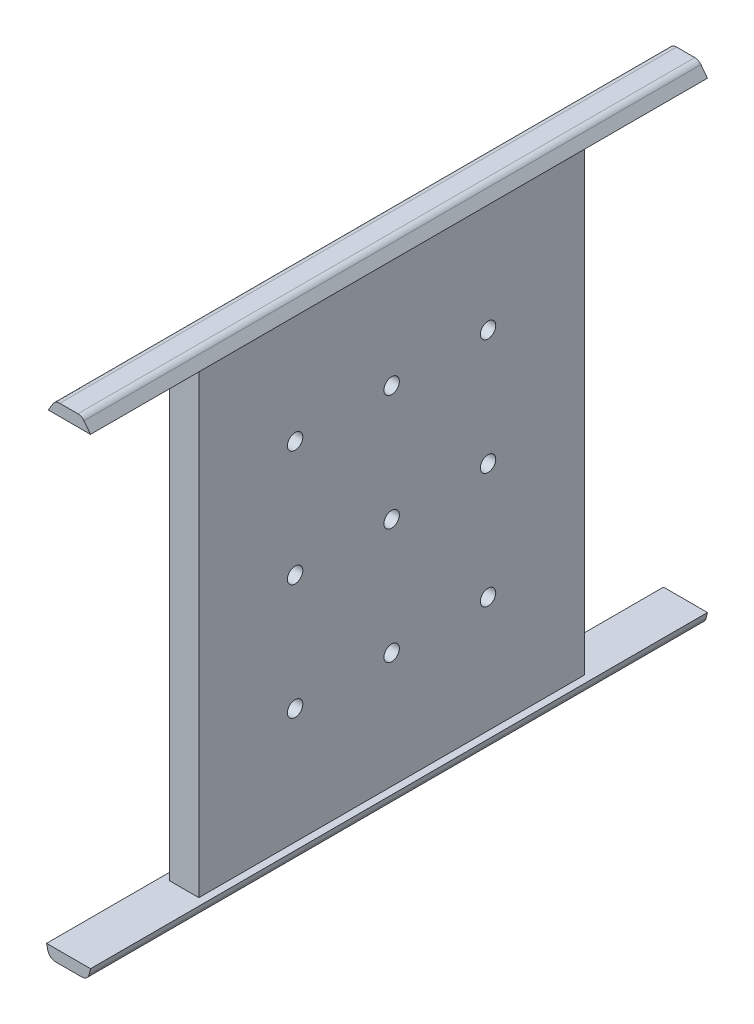
SolidWorks part; units mm, degrees
ref_plane "Plano frontal" through (0, 0, 0) normal (0, 0, 1) x (1, 0, 0)
ref_plane "Plano superior" through (0, 0, 0) normal (0, 1, 0) x (1, 0, 0)
ref_plane "Plano direito" through (0, 0, 0) normal (1, 0, 0) x (0, 0, -1)
sketch "Esboço1" plane through (0, 0, 0) normal (0, 0, 1) x (1, 0, 0)
  line L0 (0, 0) -> (0, 14.1176) construction
  line L1 (-3.8, -98.1786) -> (-5.7, -98.1786)
  line L2 (0, -101.1786) -> (0, -98.1786) construction
  line L3 (0, -98.1786) -> (-3.8, -98.1786) construction
  line L4 (-3.4129, -101.1786) -> (3.4129, -101.1786)
  line L5 (3.8, -98.1786) -> (0, -98.1786) construction
  line L6 (5.7, -98.1786) -> (5.7, -30.5351) construction
  line L7 (-5.3606, -99.6331) -> (-5.7, -98.1786)
  line L8 (5.7, -98.1786) -> (5.3606, -99.6331)
  line L9 (5.7, -30.5351) -> (5.7, 21.8214) construction
  line L10 (5.7, 21.8214) -> (3.4129, 21.8214) construction
  line L11 (3.8, -98.1786) -> (3.8, 21.8214)
  line L12 (3.8, 21.8214) -> (3.4129, 21.8214)
  line L13 (-3.8, -98.1786) -> (-3.8, 21.8214)
  line L14 (3.8, -98.1786) -> (5.7, -98.1786)
  line L15 (-5.2668, 21.8214) -> (-5.2668, 17.6583) construction
  line L16 (3.4129, -101.1786) -> (3.4129, 21.8214) construction
  line L17 (-3.4129, -101.1786) -> (-3.4129, 24.8214) construction
  line L18 (5.7, 21.8214) -> (3.4129, 21.8214)
  line L19 (3.4129, 21.8214) -> (3.4129, 24.8214) construction
  line L20 (5.7, 21.8214) -> (4.0133, 24.0339)
  line L21 (2.4227, 24.8214) -> (-2.2978, 24.8214)
  line L22 (-3.9992, 23.8727) -> (-5.2668, 21.8214)
  line L23 (-3.4129, 21.8214) -> (-5.2668, 21.8214) construction
  line L24 (-3.4129, 21.8214) -> (-3.8, 21.8214)
  line L25 (-3.4129, 21.8214) -> (-5.2668, 21.8214)
  arc A0 (3.4129, -101.1786) -> (5.3606, -99.6331) centre (3.4129, -99.1786) ccw
  arc A1 (-5.3606, -99.6331) -> (-3.4129, -101.1786) centre (-3.4129, -99.1786) ccw
  arc A2 (-2.2978, 24.8214) -> (-3.9992, 23.8727) centre (-2.2978, 22.8214) ccw
  arc A3 (2.4227, 24.8214) -> (4.0133, 24.0339) centre (2.4227, 22.8214) cw
  point P15 (5, -101.1786)
  point P18 (-5, -101.1786)
  dimension "D9" = 2
  dimension "D11" = 2
  dimension "D1" = 5.7
  dimension "D2" = 5.7
  dimension "D3" = 11.4
  dimension "D4" = 5.7
  dimension "D5" = 5
  dimension "D6" = 7.6
  dimension "D7" = 3.8
  dimension "D8" = 120
  dimension "D10" = 3
  dimension "D12" = 3
extrude "Ressalto-extrusão1" add sketch "Esboço1" along normal blind 160
sketch "Esboço2" plane through (0, 0, 0) normal (0, 0, 1) x (1, 0, 0)
  line L1 (-3.8, 21.8214) -> (3.8, 21.8214)
  line L2 (-3.8, 21.8214) -> (-3.8, -98.1786)
  line L3 (-3.8, -98.1786) -> (3.8, -98.1786)
  line L4 (3.8, 21.8214) -> (3.8, -98.1786)
extrude "Corte-extrusão1" cut sketch "Esboço2" along normal blind 30
sketch3d "3DSketch2"
  line L1 (-3.8, 21.8214, 160) -> (3.8, 21.8214, 160)
  line L2 (-3.8, 21.8214, 160) -> (-3.8, -98.1786, 160)
  line L3 (-3.8, -98.1786, 160) -> (3.8, -98.1786, 160)
  line L4 (3.8, 21.8214, 160) -> (3.8, -98.1786, 160)
  dimension "D1" = 160
extrude "Corte-extrusão2" cut sketch "3DSketch2" along direction (0, 0, 1) on the side of the normal blind 30
sketch3d "3DSketch3"
  line L0 (3.8, 21.8214, 130) -> (3.8, 21.8214, 80) construction
  line L1 (3.8, 21.8214, 130) -> (3.8, 21.8214, 30) construction
  line L2 (3.8, 21.8214, 80) -> (3.8, -98.1786, 80) construction
  line L3 (3.8, -98.1786, 130) -> (3.8, -98.1786, 30) construction
  line L4 (3.8, -98.1786, 80) -> (3.8, -98.1786, 130) construction
  line L5 (3.8, -98.1786, 130) -> (3.8, -38.1786, 130) construction
  line L6 (3.8, -98.1786, 130) -> (3.8, 21.8214, 130) construction
  line L7 (3.8, -38.1786, 130) -> (3.8, -38.1786, 30) construction
  line L8 (3.8, -98.1786, 30) -> (3.8, 21.8214, 30) construction
  line L9 (3.8, 21.8214, 130) -> (3.8, -98.1786, 30) construction
  line L10 (3.8, -98.1786, 30) -> (3.8, -98.1786, 130) construction
  line L11 (3.8, -98.1786, 130) -> (3.8, 21.8214, 30) construction
  line L12 (3.8, 21.8214, 30) -> (3.8, -38.1786, 130) construction
  line L13 (3.8, -38.1786, 130) -> (3.8, 21.8214, 130) construction
  line L14 (3.8, 21.8214, 130) -> (3.8, -38.1786, 30) construction
  line L15 (3.8, -38.1786, 30) -> (3.8, -8.1786, 30) construction
  line L16 (3.8, -8.1786, 30) -> (3.8, -8.1786, 130) construction
  line L17 (3.8, -38.1786, 130) -> (3.8, -98.1786, 30) construction
  line L18 (3.8, -98.1786, 30) -> (3.8, -98.1786, 130) construction
  line L19 (3.8, -98.1786, 130) -> (3.8, -38.1786, 30) construction
  line L20 (3.8, -68.1786, 80) -> (3.8, -68.1786, 30) construction
  line L21 (3.8, -68.1786, 30) -> (3.8, -68.1786, 130) construction
  line L22 (3.8, 21.8214, 105) -> (3.8, -98.1786, 80) construction
  line L23 (3.8, -98.1786, 80) -> (3.8, -98.1786, 105) construction
  line L24 (3.8, -98.1786, 105) -> (3.8, 21.8214, 80) construction
  line L25 (3.8, 21.8214, 80) -> (3.8, -98.1786, 55) construction
  line L26 (3.8, -98.1786, 55) -> (3.8, 21.8214, 55) construction
  line L27 (3.8, 21.8214, 55) -> (3.8, -98.1786, 80) construction
  line L28 (3.8, -98.1786, 80) -> (3.8, -38.1786, 67.5) construction
  line L29 (3.8, -38.1786, 67.5) -> (3.8, -98.1786, 67.5) construction
  line L30 (3.8, -98.1786, 67.5) -> (3.8, 21.8214, 67.5) construction
  line L31 (3.8, -38.1786, 92.5213) -> (3.8, 21.8214, 92.5213) construction
  line L32 (3.8, 21.8214, 92.5213) -> (3.8, -98.1786, 92.5213) construction
  circle A0 centre (3.8, -38.1786, 80) radius 2
  circle A1 centre (3.8, -8.1786, 80) radius 2
  circle A2 centre (3.8, -68.1786, 80) radius 2
  circle A3 centre (3.8, -68.1786, 55) radius 2
  circle A4 centre (3.8, -38.1786, 55) radius 2
  circle A5 centre (3.8, -8.1786, 55) radius 2
  circle A6 centre (3.8, -68.1786, 105.0426) radius 2
  circle A7 centre (3.8, -38.1786, 105.0426) radius 2
  circle A8 centre (3.8, -8.1786, 105.0426) radius 2
  point P18 (5.8, -38.1786, 80)
  point P27 (5.8, -8.1786, 80)
  point P32 (5.8, -68.1786, 80)
  point P42 (5.8, -68.1786, 55)
  point P45 (5.8, -38.1786, 55)
  point P48 (5.8, -8.1786, 55)
  point P54 (5.8, -68.1786, 105.0426)
  point P57 (5.8, -38.1786, 105.0426)
  point P60 (5.8, -8.1786, 105.0426)
extrude "Corte-extrusão3" cut sketch "3DSketch3" along direction (-1, 0, 0) on the side against the normal blind 70
